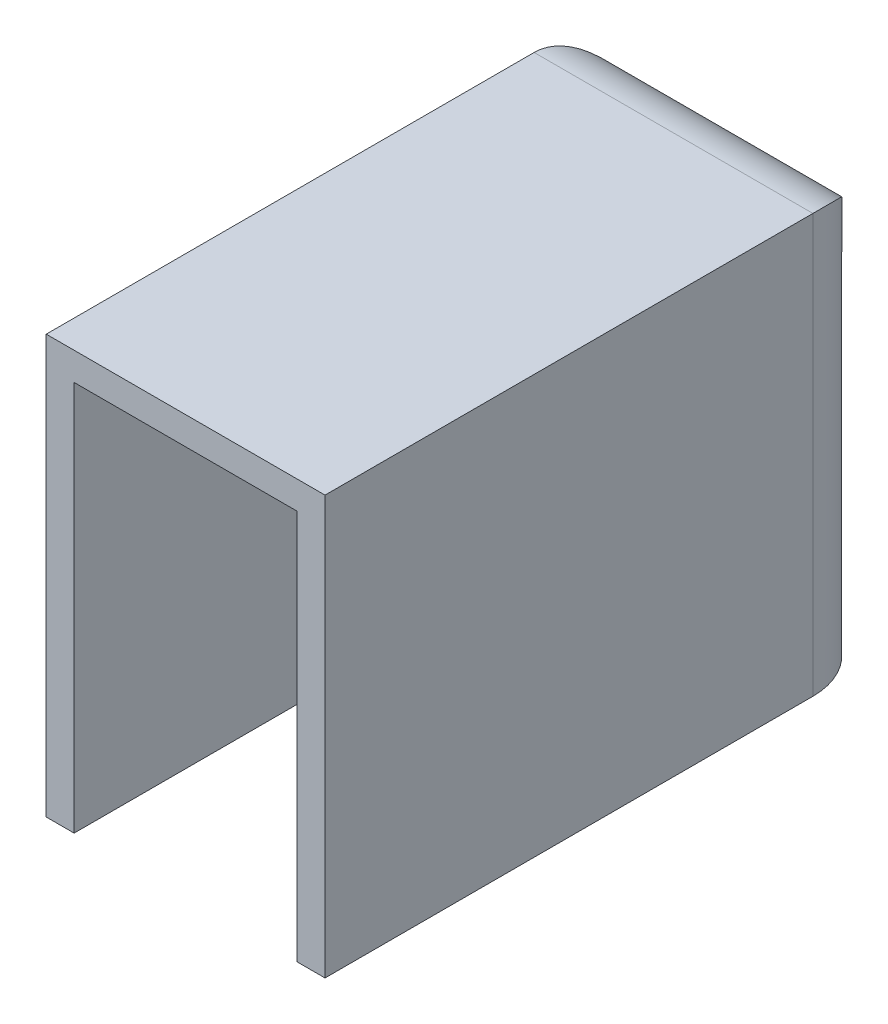
SolidWorks part; units mm, degrees
ref_plane "Płaszczyzna przednia" through (0, 0, 0) normal (0, 0, 1) x (1, 0, 0)
ref_plane "Płaszczyzna górna" through (0, 0, 0) normal (0, 1, 0) x (1, 0, 0)
ref_plane "Płaszczyzna prawa" through (0, 0, 0) normal (1, 0, 0) x (0, 0, -1)
sketch "Szkic1" plane through (0, 0, 0) normal (0, 0, 1) x (1, 0, 0)
  line L1 (-10, -15) -> (10, -15)
  line L2 (-10, -15) -> (-10, 15)
  line L3 (-10, 15) -> (10, 15)
  line L4 (10, -15) -> (10, 15)
  line L5 (-10, -15) -> (10, 15) construction
  line L6 (-10, 15) -> (10, -15) construction
  point P0 (0, 0)
  dimension "D1" = 20
  dimension "D2" = 30
extrude "Dodanie-wyciągnięcie1" add sketch "Szkic1" along normal blind 40
shell "Skorupa3" thickness 2
fillet "Zaokrąglenie1" radius 5 3 edges at (-10, 0, 0) (0, 15, 0) (10, 0, 0)
sketch "Szkic2" plane through (0, 0, 2) normal (0, 0, 1) x (1, 0, 0)
  line L0 (-8, -15) -> (8, -15) construction
  line L1 (6, -10) -> (-6, -10)
  line L2 (6, -10) -> (6, -12)
  line L3 (6, -12) -> (-6, -12)
  line L4 (-6, -10) -> (-6, -12)
  line L5 (6, -10) -> (-6, -12) construction
  line L6 (6, -12) -> (-6, -10) construction
  line L7 (8, -15) -> (8, 13) construction
  point P0 (0, -11)
  dimension "D1" = 3
  dimension "D2" = 2
  dimension "D3" = 12
  dimension "D4" = 2
extrude "Dodanie-wyciągnięcie2" add sketch "Szkic2" along normal blind 2.5
